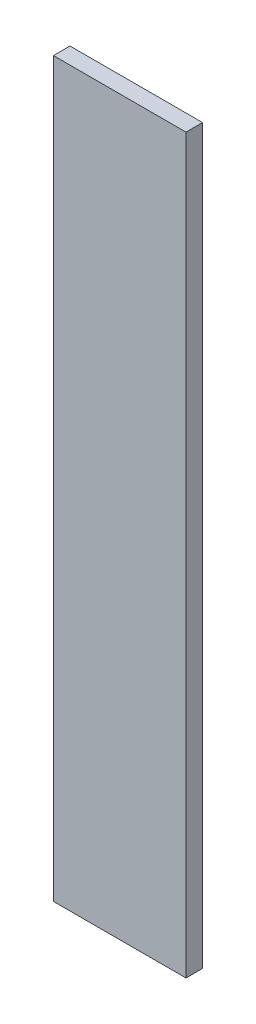
SolidWorks part; units mm, degrees
material "ABS"
ref_plane "Front Plane" through (0, 0, 0) normal (0, 0, 1) x (1, 0, 0)
ref_plane "Top Plane" through (0, 0, 0) normal (0, 1, 0) x (1, 0, 0)
ref_plane "Right Plane" through (0, 0, 0) normal (1, 0, 0) x (0, 0, -1)
sketch "Sketch1" plane through (0, 0, 0) normal (0, 0, 1) x (1, 0, 0)
  line L1 (-40, 221) -> (40, 221)
  line L2 (-40, 221) -> (-40, -221)
  line L3 (-40, -221) -> (40, -221)
  line L4 (40, 221) -> (40, -221)
  line L5 (-40, 221) -> (40, -221) construction
  line L6 (-40, -221) -> (40, 221) construction
  point P0 (0, 0)
  dimension "D1" = 442
  dimension "D2" = 80
extrude "Boss-Extrude1" add sketch "Sketch1" along normal mid plane 10
